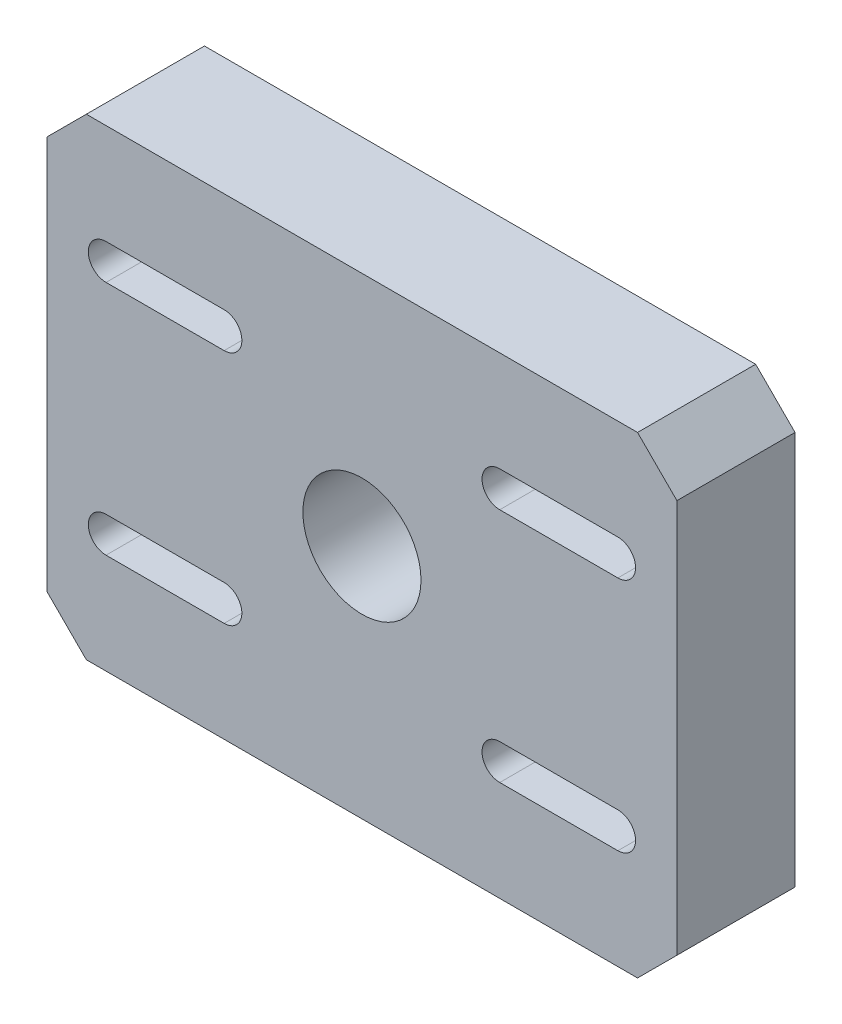
SolidWorks part; units mm, degrees
ref_plane "前视基准面" through (0, 0, 0) normal (0, 0, 1) x (1, 0, 0)
ref_plane "上视基准面" through (0, 0, 0) normal (0, 1, 0) x (1, 0, 0)
ref_plane "右视基准面" through (0, 0, 0) normal (1, 0, 0) x (0, 0, -1)
sketch "草图1" plane through (0, 0, 0) normal (0, 0, 1) x (1, 0, 0)
  line L1 (80, -60) -> (-80, -60)
  line L2 (80, -60) -> (80, 60)
  line L3 (80, 60) -> (-80, 60)
  line L4 (-80, -60) -> (-80, 60)
  line L5 (80, -60) -> (-80, 60) construction
  line L6 (80, 60) -> (-80, -60) construction
  point P0 (0, 0)
  dimension "D1" = 120
  dimension "D2" = 160
extrude "凸台-拉伸1" add sketch "草图1" along normal blind 30
sketch "草图2" plane through (0, 0, 30) normal (0, 0, 1) x (1, 0, 0)
  line L0 (-65, 30) -> (-35, 30) construction
  line L1 (50, -30) -> (-50, -30) construction
  line L2 (50, -30) -> (50, 30) construction
  line L3 (50, 30) -> (-50, 30) construction
  line L4 (-50, -30) -> (-50, 30) construction
  line L5 (50, -30) -> (-50, 30) construction
  line L6 (50, 30) -> (-50, -30) construction
  line L7 (-65, 34.5) -> (-35, 34.5)
  line L8 (-65, 25.5) -> (-35, 25.5)
  line L9 (65, 30) -> (35, 30) construction
  line L10 (65, 25.5) -> (35, 25.5)
  line L11 (65, 34.5) -> (35, 34.5)
  line L12 (-65, -30) -> (-35, -30) construction
  line L13 (-65, -25.5) -> (-35, -25.5)
  line L14 (-65, -34.5) -> (-35, -34.5)
  line L15 (65, -30) -> (35, -30) construction
  line L16 (65, -34.5) -> (35, -34.5)
  line L17 (65, -25.5) -> (35, -25.5)
  arc A0 (-65, 34.5) -> (-65, 25.5) centre (-65, 30) ccw
  arc A1 (-35, 25.5) -> (-35, 34.5) centre (-35, 30) ccw
  arc A2 (65, 25.5) -> (65, 34.5) centre (65, 30) ccw
  arc A3 (35, 34.5) -> (35, 25.5) centre (35, 30) ccw
  arc A4 (-65, -25.5) -> (-65, -34.5) centre (-65, -30) ccw
  arc A5 (-35, -34.5) -> (-35, -25.5) centre (-35, -30) ccw
  arc A6 (65, -34.5) -> (65, -25.5) centre (65, -30) ccw
  arc A7 (35, -25.5) -> (35, -34.5) centre (35, -30) ccw
  point P0 (0, 0)
  point P8 (-50, 30)
  point P14 (50, 30)
  point P21 (-50, -30)
  point P28 (50, -30)
  dimension "D3" = 4.5
  dimension "D1" = 100
  dimension "D2" = 60
  dimension "D4" = 30
extrude "切除-拉伸1" cut sketch "草图2" against normal through all
chamfer "倒角1" distance 10 angle 45 4 edges at (80, -60, 15) (80, 60, 15) (-80, -60, 15) (-80, 60, 15)
sketch "草图3" plane through (0, 0, 30) normal (0, 0, 1) x (1, 0, 0)
  circle A0 centre (0, 0) radius 15
extrude "切除-拉伸2" cut sketch "草图3" against normal blind 30
